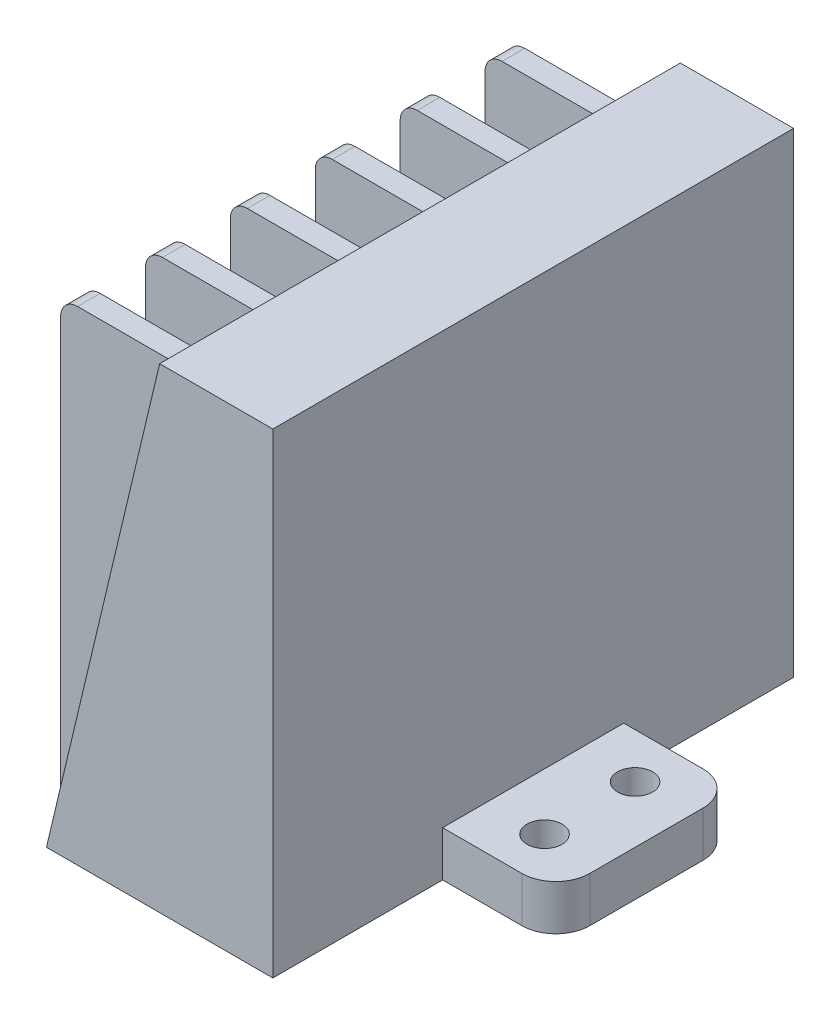
SolidWorks part; units mm, degrees
ref_plane "Front" through (0, 0, 0) normal (0, 0, 1) x (1, 0, 0)
ref_plane "Top" through (0, 0, 0) normal (0, 1, 0) x (1, 0, 0)
ref_plane "Right" through (0, 0, 0) normal (1, 0, 0) x (0, 0, -1)
sketch "Sketch1" plane through (0, 0, 0) normal (0, 0, 1) x (1, 0, 0)
  line L0 (0, 0) -> (0, 42)
  line L1 (0, 42) -> (-10, 42)
  line L2 (-10, 42) -> (-20, 0)
  line L3 (-20, 0) -> (0, 0)
  dimension "D1" = 42
  dimension "D2" = 10
  dimension "D3" = 20
extrude "Boss-Extrude1" add sketch "Sketch1" along normal blind 46
ref_plane "Plane1" through (0, 0, 42.75) normal (0, 0, 1) x (1, 0, 0)
sketch "Sketch2" plane through (0, 0, 42.75) normal (0, 0, 1) x (1, 0, 0)
  line L0 (-10.5952, 39.5) -> (-20.5, 39.5)
  line L1 (-10, 42) -> (-20, 0) construction
  line L2 (-20, 0) -> (-20.5, 0)
  line L3 (-22, 1.5) -> (-22, 38)
  line L4 (0, 42) -> (-10, 42) construction
  line L5 (-10.5952, 39.5) -> (-20, 0)
  arc A0 (-20.5, 39.5) -> (-22, 38) centre (-20.5, 38) ccw
  arc A1 (-22, 1.5) -> (-20.5, 0) centre (-20.5, 1.5) ccw
  dimension "D3" = 1.5
  dimension "D4" = 1.5
  dimension "D1" = 2.5
  dimension "D2" = 2
extrude "Boss-Extrude2" add sketch "Sketch2" against normal blind 2
pattern_linear "LPattern1" count 6 spacing 7.5 along (0, 0, -1) of "Boss-Extrude2"
ref_plane "Plane2" through (0, 0, 23) normal (0, 0, 1) x (1, 0, 0)
sketch "Sketch3" plane through (0, 0, 23) normal (0, 0, 1) x (1, 0, 0)
  line L8 (0, 0) -> (10, 0)
  line L9 (0, 0) -> (0, 4)
  line L10 (0, 4) -> (10, 4)
  line L11 (10, 0) -> (10, 4)
  line L12 (0, 0) -> (10, 4) construction
  line L13 (0, 4) -> (10, 0) construction
  point P4 (5, 2)
  dimension "D1" = 4
  dimension "D2" = 10
extrude "Boss-Extrude3" add sketch "Sketch3" along normal mid plane 16
sketch "Sketch4" plane through (0, 4, 0) normal (0, 1, 0) x (1, 0, 0)
  line L0 (10, -31) -> (10, -15) construction
  line L1 (10, -15) -> (0, -15) construction
  line L2 (10, -31) -> (0, -31) construction
  circle A0 centre (5, -19) radius 1.55
  circle A1 centre (5, -27) radius 1.55
  dimension "D1" = 3.1
  dimension "D2" = 3.1
  dimension "D3" = 5
  dimension "D4" = 4
  dimension "D5" = 4
extrude "Cut-Extrude1" cut sketch "Sketch4" against normal up to next
fillet "Fillet1" radius 3 2 edges at (10, 2, 15) (10, 2, 31)
